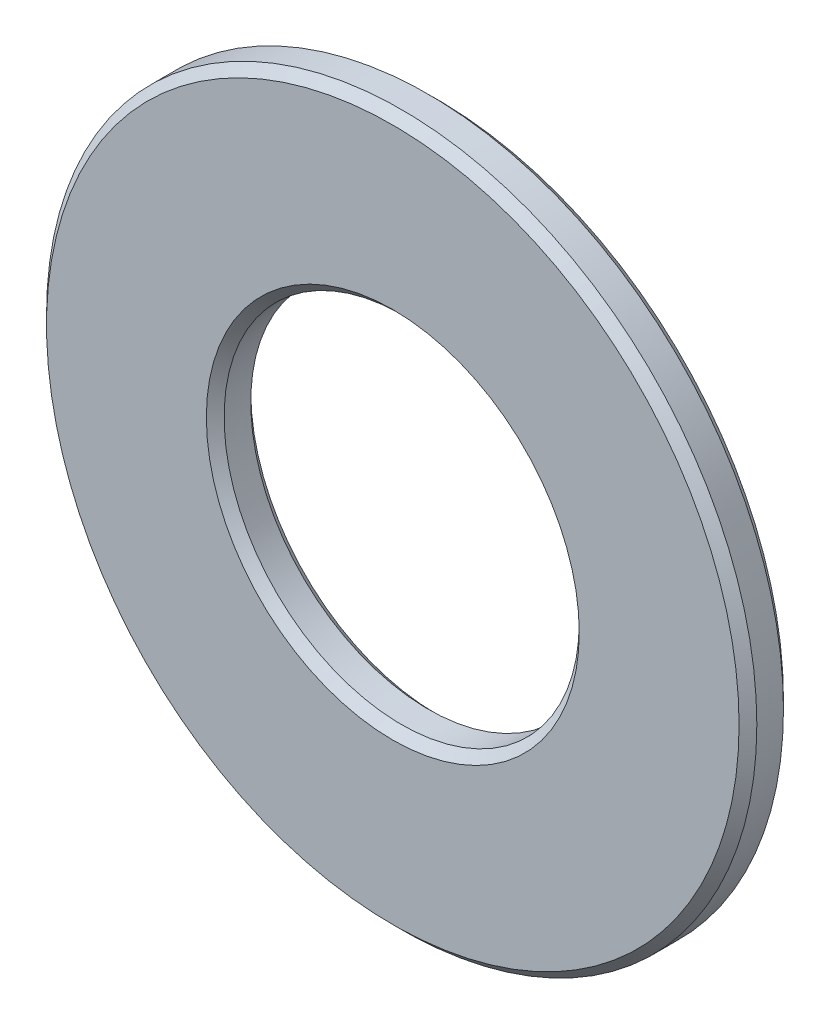
SolidWorks part; units mm, degrees
ref_plane "Спереди" through (0, 0, 0) normal (0, 0, 1) x (1, 0, 0)
ref_plane "Сверху" through (0, 0, 0) normal (0, 1, 0) x (1, 0, 0)
ref_plane "Справа" through (0, 0, 0) normal (1, 0, 0) x (0, 0, -1)
sketch "Эскиз1" plane through (0, 0, 0) normal (0, 0, 1) x (1, 0, 0)
  circle A0 centre (0, 0) radius 2
  circle A1 centre (0, 0) radius 4
extrude "Бобышка-Вытянуть1" add sketch "Эскиз1" along normal blind 0.5
chamfer "Фаска1" distance 0.1 angle 45 4 edges at (2, 0, 0) (4, 0, 0) (2, 0, 0.5) (4, 0, 0.5)
